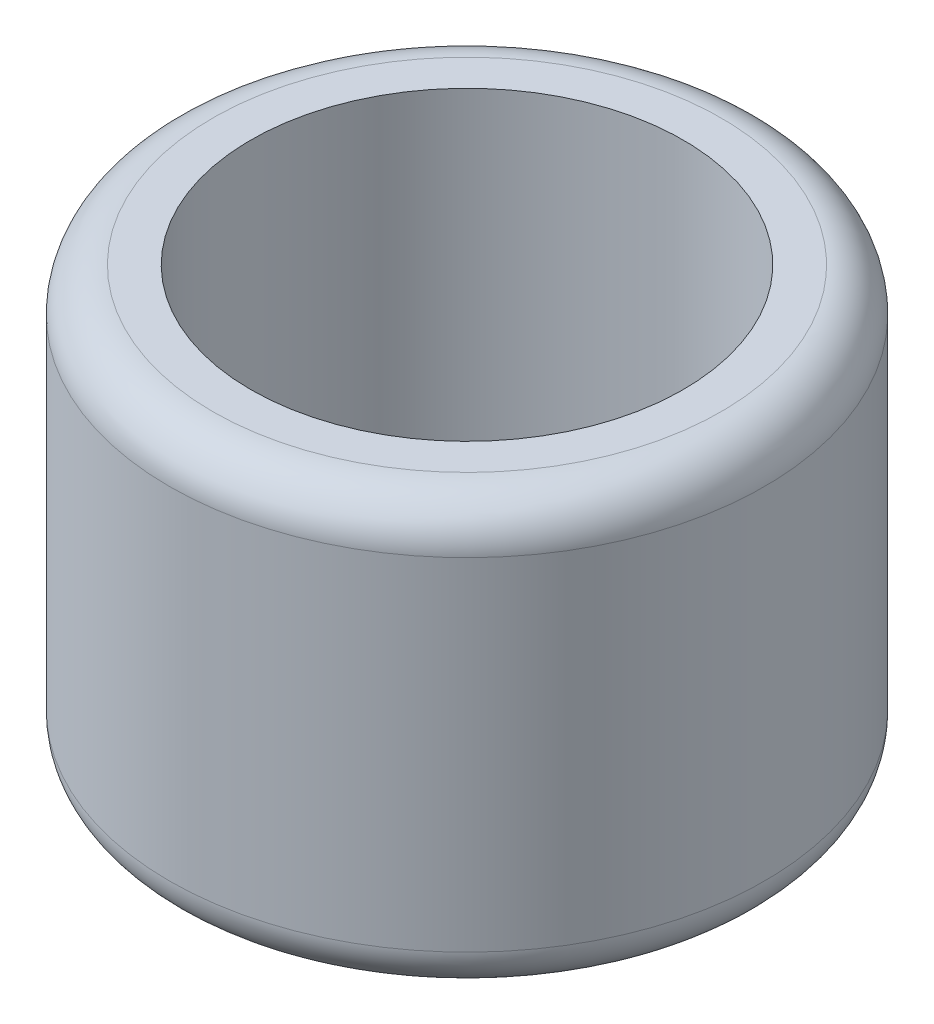
SolidWorks part; units mm, degrees
ref_plane "Front Plane" through (0, 0, 0) normal (0, 0, 1) x (1, 0, 0)
ref_plane "Top Plane" through (0, 0, 0) normal (0, 1, 0) x (1, 0, 0)
ref_plane "Right Plane" through (0, 0, 0) normal (1, 0, 0) x (0, 0, -1)
other "Bounding Box"
ref_plane "Default Plane" through (13.8565, 3.175, 6.7999) normal (0, -1, 0) x (-1, 0, 0)
sketch "Sketch1" plane through (0, 0, 0) normal (0, 1, 0) x (1, 0, 0)
  circle A0 centre (0, 0) radius 6.35
  circle A1 centre (0, 0) radius 8.7376
  dimension "D1" = 12.7
  dimension "D2" = 17.4752
extrude "Boss-Extrude1" add sketch "Sketch1" along normal mid plane 12.573
fillet "Fillet1" radius 1.27 2 edges at (0, -6.2865, 8.7376) (0, 6.2865, 8.7376)
